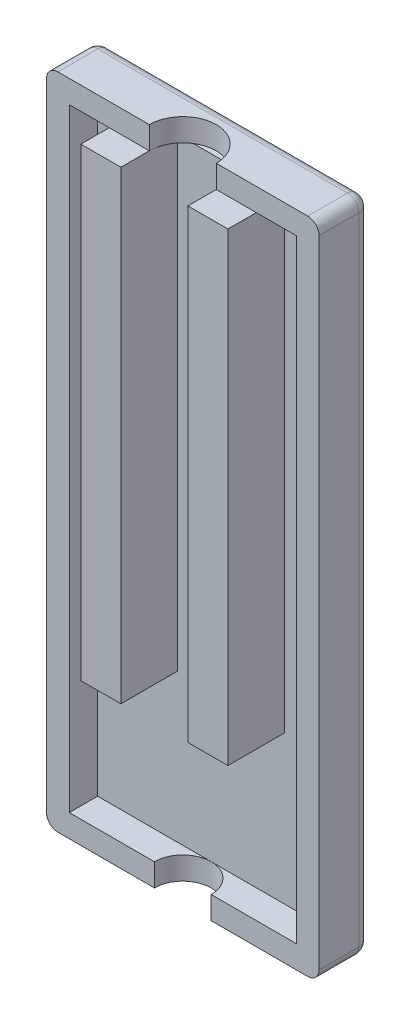
SolidWorks part; units mm, degrees
ref_plane "Front Plane" through (0, 0, 0) normal (0, 0, 1) x (1, 0, 0)
ref_plane "Top Plane" through (0, 0, 0) normal (0, 1, 0) x (1, 0, 0)
ref_plane "Right Plane" through (0, 0, 0) normal (1, 0, 0) x (0, 0, -1)
sketch "Sketch1" plane through (0, 0, 0) normal (0, 0, 1) x (1, 0, 0)
  line L1 (-12, 33) -> (12, 33)
  line L2 (-12, 33) -> (-12, -25)
  line L3 (-12, -25) -> (12, -25)
  line L4 (12, 33) -> (12, -25)
  point P0 (0, 0)
  dimension "D2" = 58
extrude "Boss-Extrude1" add sketch "Sketch1" along normal blind 2
sketch "Sketch2" plane through (0, 0, 2) normal (0, 0, 1) x (1, 0, 0)
  line L0 (12, 33) -> (-12, 33) construction
  line L2 (-12, 33) -> (-12, -25)
  line L3 (-12, -25) -> (12, -25)
  line L4 (12, 9) -> (12, -25)
  line L6 (-10, 23) -> (-10, -23)
  line L7 (-10, -23) -> (10, -23)
  line L8 (10, 23) -> (10, -23)
  line L10 (-10, 23) -> (-10, 31)
  line L11 (-10, 31) -> (10, 31)
  line L12 (10, 23) -> (10, 31)
  dimension "D1" = 2
  dimension "D2" = 2
  dimension "D3" = 2
  dimension "D4" = 2
extrude "Boss-Extrude2" add sketch "Sketch2" along normal blind 2.5
sketch "Sketch5" plane through (0, 31, 0) normal (0, -1, 0) x (1, 0, 0)
  line L0 (-12, 4.5) -> (12, 4.5) construction
  line L1 (-2.95, 4.5) -> (2.95, 4.5)
  arc A0 (-2.95, 4.5) -> (2.95, 4.5) centre (0, 4.5) ccw
  dimension "D1" = 5.9
extrude "Cut-Extrude3" cut sketch "Sketch5" against normal through all
sketch "Sketch6" plane through (0, -23, 0) normal (0, 1, 0) x (1, 0, 0)
  line L0 (-10, -4.5) -> (10, -4.5) construction
  line L1 (-2.5, -4.5) -> (2.5, -4.5)
  arc A0 (2.5, -4.5) -> (-2.5, -4.5) centre (0, -4.5) ccw
  dimension "D1" = 5
extrude "Cut-Extrude4" cut sketch "Sketch6" against normal through all
sketch "Sketch7" plane through (0, 0, 2) normal (0, 0, 1) x (1, 0, 0)
  line L0 (-2.95, 31) -> (-2.95, -9.9265)
  line L1 (-2.95, -9.9265) -> (-6.475, -9.9265)
  line L6 (-6.475, 31) -> (-2.95, 31)
  line L7 (2.95, 31) -> (2.95, -9.9265)
  line L8 (2.95, -9.9265) -> (6.475, -9.9265)
  line L11 (6.475, 31) -> (2.95, 31)
  line L12 (-6.475, 31) -> (-6.475, -9.9265)
  line L13 (6.475, 31) -> (6.475, -9.9265)
extrude "Boss-Extrude3" add sketch "Sketch7" along normal blind 5
fillet "Fillet1" radius 1 8 edges at (12, -25, 2.25) (0, -25, 0) (-12, -25, 2.25) (-12, 4, 0) (-12, 33, 2.25) (0, 33, 0) (12, 4, 0) (12, 33, 2.25)
